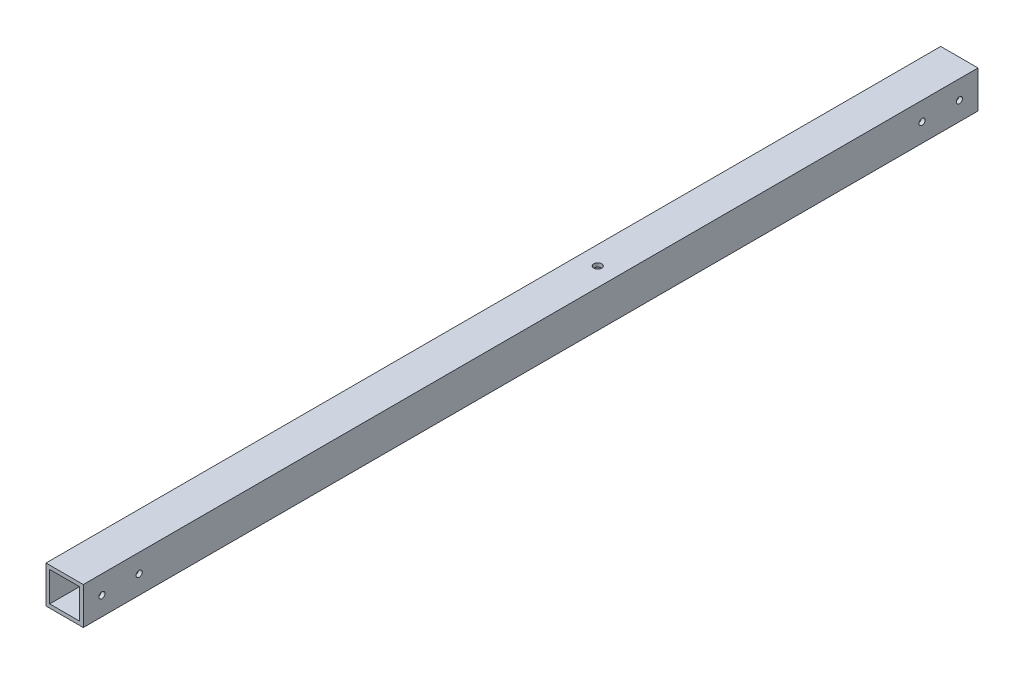
SolidWorks part; units mm, degrees
ref_plane "正面" through (0, 0, 0) normal (0, 0, 1) x (1, 0, 0)
ref_plane "平面" through (0, 0, 0) normal (0, 1, 0) x (1, 0, 0)
ref_plane "右側面" through (0, 0, 0) normal (1, 0, 0) x (0, 0, -1)
sketch "ｽｹｯﾁ1" plane through (0, 0, 0) normal (0, 0, 1) x (1, 0, 0)
  line L1 (-10, 10) -> (10, 10)
  line L2 (-10, 10) -> (-10, -10)
  line L3 (-10, -10) -> (10, -10)
  line L4 (10, 10) -> (10, -10)
  line L5 (-10, 10) -> (10, -10) construction
  line L6 (-10, -10) -> (10, 10) construction
  line L7 (-8, 8) -> (8, 8)
  line L8 (-8, 8) -> (-8, -8)
  line L9 (-8, -8) -> (8, -8)
  line L10 (8, 8) -> (8, -8)
  line L11 (-8, 8) -> (8, -8) construction
  line L12 (-8, -8) -> (8, 8) construction
  point P0 (0, 0)
  point P6 (0, 0)
  dimension "D1" = 20
  dimension "D2" = 20
  dimension "D3" = 16
  dimension "D4" = 16
extrude "ﾎﾞｽ - 押し出し1" add sketch "ｽｹｯﾁ1" along normal blind 560
sketch "ｽｹｯﾁ3" plane through (10, 0, 0) normal (1, 0, 0) x (0, 0, -1)
  line L0 (-560, 0) -> (-530, 0)
  line L1 (-560, -10) -> (-560, 10) construction
  line L2 (-530, 0) -> (-30, 0)
  circle A0 centre (-530, 0) radius 2.2
  circle A1 centre (-30, 0) radius 2.2
  dimension "D2" = 4.4
  dimension "D4" = 4.4
  dimension "D1" = 30
  dimension "D3" = 500
extrude "ｶｯﾄ - 押し出し2" cut sketch "ｽｹｯﾁ3" against normal blind 560
sketch "ｽｹｯﾁ4" plane through (0, 10, 0) normal (0, 1, 0) x (1, 0, 0)
  line L0 (0, -560) -> (0, -550)
  line L1 (10, -560) -> (-10, -560) construction
  line L2 (0, -550) -> (0, -10)
  circle A0 centre (0, -550) radius 2.2
  circle A1 centre (0, -10) radius 2.2
  dimension "D2" = 4.4
  dimension "D4" = 4.4
  dimension "D1" = 10
  dimension "D3" = 540
extrude "ｶｯﾄ - 押し出し3" cut sketch "ｽｹｯﾁ4" against normal blind 560
sketch "ｽｹｯﾁ5" plane through (0, 0, 0) normal (0, 0, -1) x (-1, 0, 0)
  line L1 (-17.7765, -27.2052) -> (17.7765, -27.2052)
  line L2 (-17.7765, -27.2052) -> (-17.7765, 27.2052)
  line L3 (-17.7765, 27.2052) -> (17.7765, 27.2052)
  line L4 (17.7765, -27.2052) -> (17.7765, 27.2052)
  line L5 (-17.7765, -27.2052) -> (17.7765, 27.2052) construction
  line L6 (-17.7765, 27.2052) -> (17.7765, -27.2052) construction
  point P0 (0, 0)
extrude "ｶｯﾄ - 押し出し4" cut sketch "ｽｹｯﾁ5" against normal blind 40
sketch "ｽｹｯﾁ6" plane through (0, 0, 560) normal (0, 0, 1) x (1, 0, 0)
  line L1 (-16.4693, 18.3609) -> (16.4693, 18.3609)
  line L2 (-16.4693, 18.3609) -> (-16.4693, -18.3609)
  line L3 (-16.4693, -18.3609) -> (16.4693, -18.3609)
  line L4 (16.4693, 18.3609) -> (16.4693, -18.3609)
  line L5 (-16.4693, 18.3609) -> (16.4693, -18.3609) construction
  line L6 (-16.4693, -18.3609) -> (16.4693, 18.3609) construction
  point P0 (0, 0)
extrude "ｶｯﾄ - 押し出し5" cut sketch "ｽｹｯﾁ6" against normal blind 40
sketch "ｽｹｯﾁ7" plane through (0, 10, 0) normal (0, 1, 0) x (1, 0, 0)
  line L0 (0, -520) -> (0, -510)
  line L1 (10, -520) -> (-10, -520) construction
  line L2 (0, -510) -> (0, -490)
  circle A0 centre (0, -510) radius 2.1
  circle A1 centre (0, -490) radius 2.1
  dimension "D3" = 4.2
  dimension "D4" = 4.2
  dimension "D1" = 10
  dimension "D2" = 20
sketch "ｽｹｯﾁ8" plane through (10, 0, 0) normal (1, 0, 0) x (0, 0, -1)
  line L0 (-520, 0) -> (-510, 0)
  line L1 (-520, -10) -> (-520, 10) construction
  line L2 (-510, 0) -> (-490, 0)
  line L3 (-40, 0) -> (-50, 0)
  line L4 (-40, -10) -> (-40, 10) construction
  line L5 (-50, 0) -> (-70, 0)
  circle A0 centre (-50, 0) radius 1
  circle A1 centre (-70, 0) radius 1
  circle A2 centre (-490, 0) radius 1
  circle A3 centre (-510, 0) radius 1
  dimension "D3" = 2
  dimension "D4" = 2
  dimension "D7" = 2
  dimension "D8" = 2
  dimension "D1" = 10
  dimension "D2" = 20
  dimension "D5" = 10
  dimension "D6" = 20
extrude "ｶｯﾄ - 押し出し7" cut sketch "ｽｹｯﾁ8" against normal blind 10
sketch "ｽｹｯﾁ9" plane through (0, -10, 0) normal (0, -1, 0) x (1, 0, 0)
  line L0 (0, 520) -> (0, 326)
  line L1 (-10, 520) -> (10, 520) construction
  circle A0 centre (0, 326) radius 2.1
  dimension "D2" = 4.2
  dimension "D1" = 194
sketch "ｽｹｯﾁ10" plane through (0, -10, 0) normal (0, -1, 0) x (1, 0, 0)
  line L0 (0, 40) -> (0, 234)
  line L2 (-10, 40) -> (10, 40) construction
  circle A0 centre (0, 234) radius 2.1
  dimension "D2" = 4.2
  dimension "D1" = 194
extrude "ｶｯﾄ - 押し出し8" cut sketch "ｽｹｯﾁ10" against normal through all
sketch "ｽｹｯﾁ11" plane through (0, -10, 0) normal (0, -1, 0) x (1, 0, 0)
  circle A0 centre (0, 234) radius 6
  dimension "D1" = 12
extrude "ｶｯﾄ - 押し出し9" cut sketch "ｽｹｯﾁ11" against normal blind 10
hole_wizard "M4x0.7 ねじ穴1" positions "3Dｽｹｯﾁ1" profile "ｽｹｯﾁ12" tap size "M4x0.7" standard "JIS"
sketch3d "3Dｽｹｯﾁ1"
  line L0 (8, 0, 50) -> (10, 0, 50) construction
  line L1 (8, 0, 70) -> (10, 0, 70) construction
  line L2 (8, 0, 490) -> (10, 0, 490) construction
  line L3 (8, 0, 510) -> (10, 0, 510) construction
  point P0 (10, 0, 50)
  point P4 (10, 0, 70)
  point P8 (10, 0, 490)
  point P12 (10, 0, 510)
sketch "ｽｹｯﾁ12" plane through (10, 0, 50) normal (0, 1, 0) x (0, 0, -1)
  line L0 (0, 0) -> (0, 12.4914)
  line L1 (0, 12.4914) -> (1.65, 11.5)
  line L2 (1.65, 11.5) -> (1.65, 0)
  line L5 (1.65, 0) -> (0, 0)
  line L10 (0, 12.4914) -> (-1.65, 11.5) construction
  line L11 (0, -6.35) -> (0, 107.95) construction
  dimension "ねじ下穴ﾄﾞﾘﾙ直径" = 3.3
  dimension "ねじ下穴ﾄﾞﾘﾙの深さ" = 11.5
  dimension "ﾄﾞﾘﾙ角度" = 118
cosmetic thread "穴のねじ山1" parameters "D1"=2, "D2"=4
cosmetic thread "穴のねじ山2" parameters "D1"=2, "D2"=4
cosmetic thread "穴のねじ山3" parameters "D1"=2, "D2"=4
cosmetic thread "穴のねじ山4" parameters "D1"=2, "D2"=4
